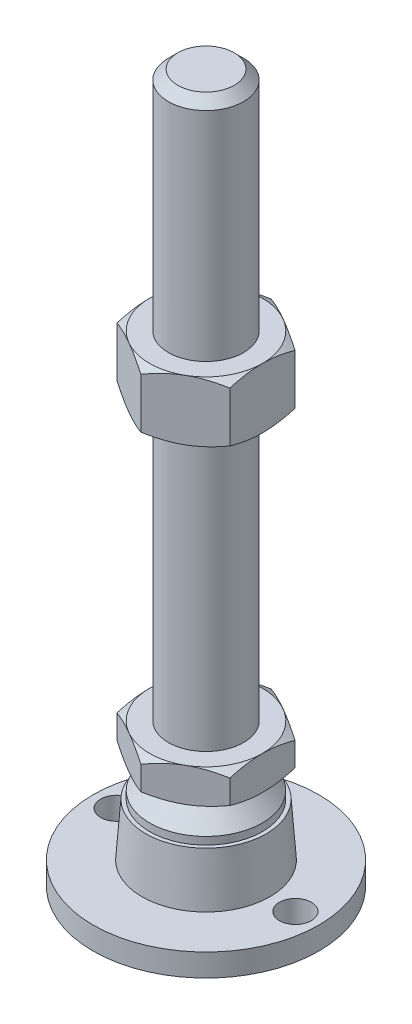
SolidWorks part; units mm, degrees
ref_plane "Спереди" through (0, 0, 0) normal (0, 0, 1) x (1, 0, 0)
ref_plane "Сверху" through (0, 0, 0) normal (0, 1, 0) x (1, 0, 0)
ref_plane "Справа" through (0, 0, 0) normal (1, 0, 0) x (0, 0, -1)
sketch "Эскиз1" plane through (0, 0, 0) normal (0, 0, 1) x (1, 0, 0)
  line L0 (0, 0) -> (-30, 0)
  line L3 (-30, 0) -> (-30, 6)
  line L12 (-10, 38) -> (-10, 185.5)
  line L13 (-10, 185.5) -> (-7.5, 188)
  line L14 (-7.5, 188) -> (0, 188)
  line L15 (0, 188) -> (0, 0) construction
  line L16 (-30, 6) -> (-17, 6)
  line L17 (0, 0) -> (0, 188)
  line L18 (0, 0) -> (0, -7.9595) construction
  line L19 (-10, 38) -> (-10, 29)
  line L21 (-15, 20) -> (-16, 20)
  line L22 (-17, 6) -> (-16, 20)
  line L23 (-15, 20) -> (-15, 22)
  line L24 (-15, 22) -> (-10, 27)
  line L25 (-10, 27) -> (-10, 29)
  line L26 (-10, 38) -> (0, 38) construction
  point P8 (-10, 111.75)
revolve "Повернуть1" add sketch "Эскиз1" angle 360 about L17
ref_plane "Плоскость2" through (0, 29, 0) normal (0, 1, 0) x (1, 0, 0)
sketch "Эскиз2" plane through (0, 29, 0) normal (0, 1, 0) x (1, 0, 0)
  line L1 (0, 17.3205) -> (-15, 8.6603)
  line L2 (-15, 8.6603) -> (-15, -8.6603)
  line L3 (-15, -8.6603) -> (0, -17.3205)
  line L4 (0, -17.3205) -> (15, -8.6603)
  line L5 (15, -8.6603) -> (15, 8.6603)
  line L6 (15, 8.6603) -> (0, 17.3205)
  circle A0 centre (0, 0) radius 15 construction
  dimension "D1" = 30
extrude "Бобышка-Вытянуть1" add sketch "Эскиз2" along normal up to vertex (9 mm away) up to point (-10, 38, 0)
ref_plane "Плоскость1" through (0, 111.75, 0) normal (0, 1, 0) x (1, 0, 0)
sketch "Эскиз3" plane through (0, 111.75, 0) normal (0, 1, 0) x (1, 0, 0)
  line L6 (15, 8.6603) -> (0, 17.3205)
  line L7 (0, 17.3205) -> (-15, 8.6603)
  line L8 (-15, 8.6603) -> (-15, -8.6603)
  line L9 (-15, -8.6603) -> (0, -17.3205)
  line L10 (0, -17.3205) -> (15, -8.6603)
  line L11 (15, -8.6603) -> (15, 8.6603)
  line L12 (15, 8.6603) -> (0, 17.3205)
  line L13 (0, 17.3205) -> (-15, 8.6603)
  line L14 (-15, 8.6603) -> (-15, -8.6603)
  line L15 (-15, -8.6603) -> (0, -17.3205)
  line L16 (0, -17.3205) -> (15, -8.6603)
  line L17 (15, -8.6603) -> (15, 8.6603)
  dimension "D1" = 0
extrude "Бобышка-Вытянуть2" add sketch "Эскиз3" along normal blind 16
sketch "Эскиз4" plane through (0, 0, 0) normal (0, 0, 1) x (1, 0, 0)
  line L0 (-15, 127.75) -> (-28.8564, 119.75)
  line L1 (-28.8564, 119.75) -> (-28.8564, 127.75)
  line L2 (-28.8564, 127.75) -> (-15, 127.75)
  line L3 (-28.8564, 119.75) -> (-15, 111.75)
  line L4 (50, 111.75) -> (-50, 111.75) construction
  line L5 (-15, 111.75) -> (-28.8564, 111.75)
  line L6 (-28.8564, 111.75) -> (-28.8564, 119.75)
  line L7 (-15, 127.75) -> (-15, 111.75) construction
  line L8 (-15, 38) -> (-22.7942, 38)
  line L9 (-22.7942, 38) -> (-22.7942, 33.5)
  line L10 (-22.7942, 33.5) -> (-15, 38)
  line L11 (-15, 29) -> (-22.7942, 33.5)
  line L12 (-22.7942, 33.5) -> (-22.7942, 29)
  line L13 (-22.7942, 29) -> (-15, 29)
  line L14 (0, 188) -> (0, 96.3793) construction
  line L15 (50, 29) -> (-50, 29) construction
  dimension "D1" = 30
  dimension "D2" = 30
revolve "Вырез-Повернуть2" cut sketch "Эскиз4" angle 360 about L14
sketch "Эскиз5" plane through (0, 6, 0) normal (0, 1, 0) x (1, 0, 0)
  line L0 (23.75, 0) -> (-23.75, 0) construction
  circle A0 centre (-23.75, 0) radius 4.25
  circle A1 centre (23.75, 0) radius 4.25
  circle A2 centre (0, 0) radius 30 construction
  dimension "D1" = 8.5
  dimension "D2" = 2
extrude "Вырез-Вытянуть1" cut sketch "Эскиз5" against normal through all
equation "\"D13@Эскиз1\"=\"D12@Эскиз1\"/2"
